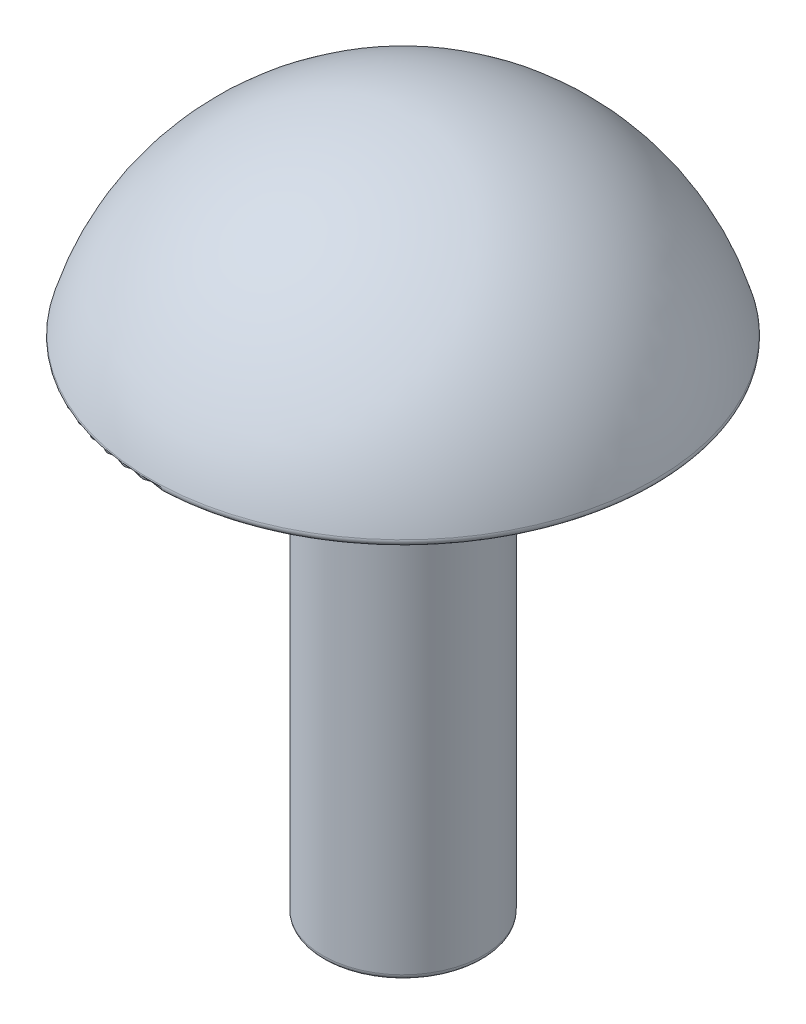
SolidWorks part; units mm, degrees
ref_plane "Front Plane" through (0, 0, 0) normal (0, 0, 1) x (1, 0, 0)
ref_plane "Top Plane" through (0, 0, 0) normal (0, 1, 0) x (1, 0, 0)
ref_plane "Right Plane" through (0, 0, 0) normal (1, 0, 0) x (0, 0, -1)
sketch "Sketch1" plane through (0, 0, 0) normal (0, 0, 1) x (1, 0, 0)
  line L0 (0, 3.5606) -> (0, -9.4394)
  line L1 (0, -9.4394) -> (1.5, -9.4394)
  line L2 (1.5, -9.4394) -> (1.5, -0.1394)
  line L3 (1.5, -0.1394) -> (4.75, -0.1394)
  arc A0 (0, 3.5606) -> (4.75, -0.1394) centre (0, -1.3384) cw
  dimension "D1" = 1.5
  dimension "D2" = 4.75
  dimension "D3" = 13
  dimension "D4" = 9.3
revolve "Revolve1" add sketch "Sketch1" angle 360 about L0
fillet "Fillet2" radius 0.1 3 edges at (-4.75, -0.1394, 0) (-1.5, -9.4394, 0) (-1.5, -0.1394, 0)
